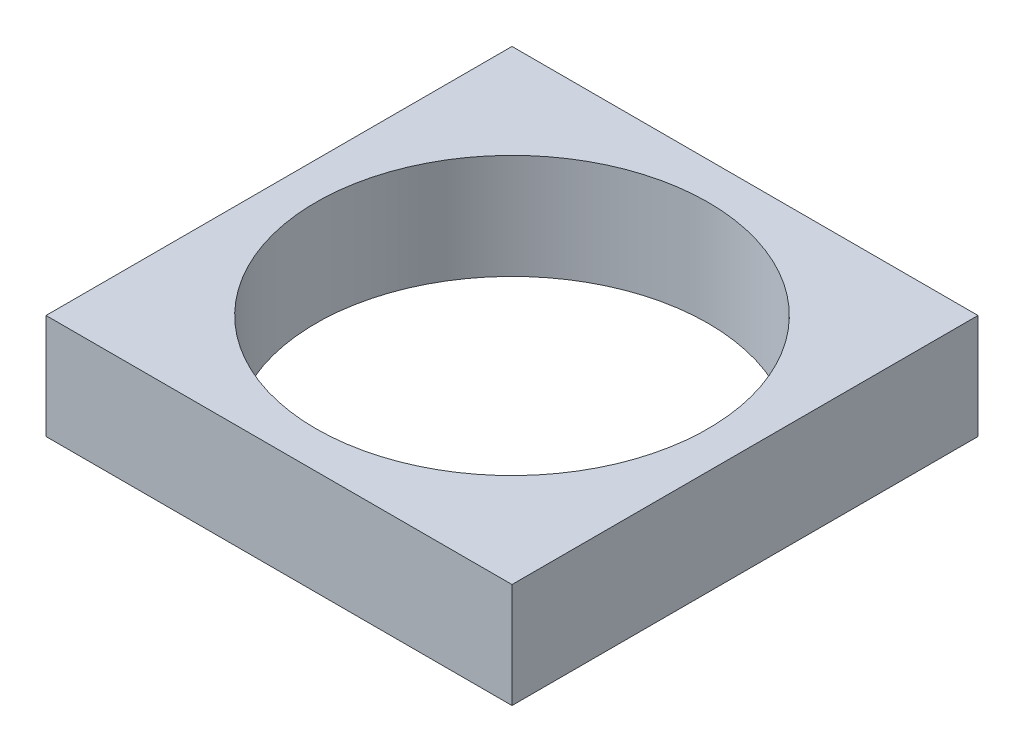
SolidWorks part; units mm, degrees
ref_plane "前视基准面" through (0, 0, 0) normal (0, 0, 1) x (1, 0, 0)
ref_plane "上视基准面" through (0, 0, 0) normal (0, 1, 0) x (1, 0, 0)
ref_plane "右视基准面" through (0, 0, 0) normal (1, 0, 0) x (0, 0, -1)
other "Configuration Table"
sketch "草图1" plane through (0, 0, 0) normal (0, 1, 0) x (1, 0, 0)
  line L1 (-6, 6) -> (6, 6)
  line L2 (-6, 6) -> (-6, -6)
  line L3 (-6, -6) -> (6, -6)
  line L4 (6, 6) -> (6, -6)
  line L5 (-6, 6) -> (6, -6) construction
  line L6 (-6, -6) -> (6, 6) construction
  circle A0 centre (0, 0) radius 5.05
  point P0 (0, 0)
  dimension "D1" = 10.1
  dimension "D2" = 12
extrude "凸台-拉伸1" add sketch "草图1" along normal blind 2.7
